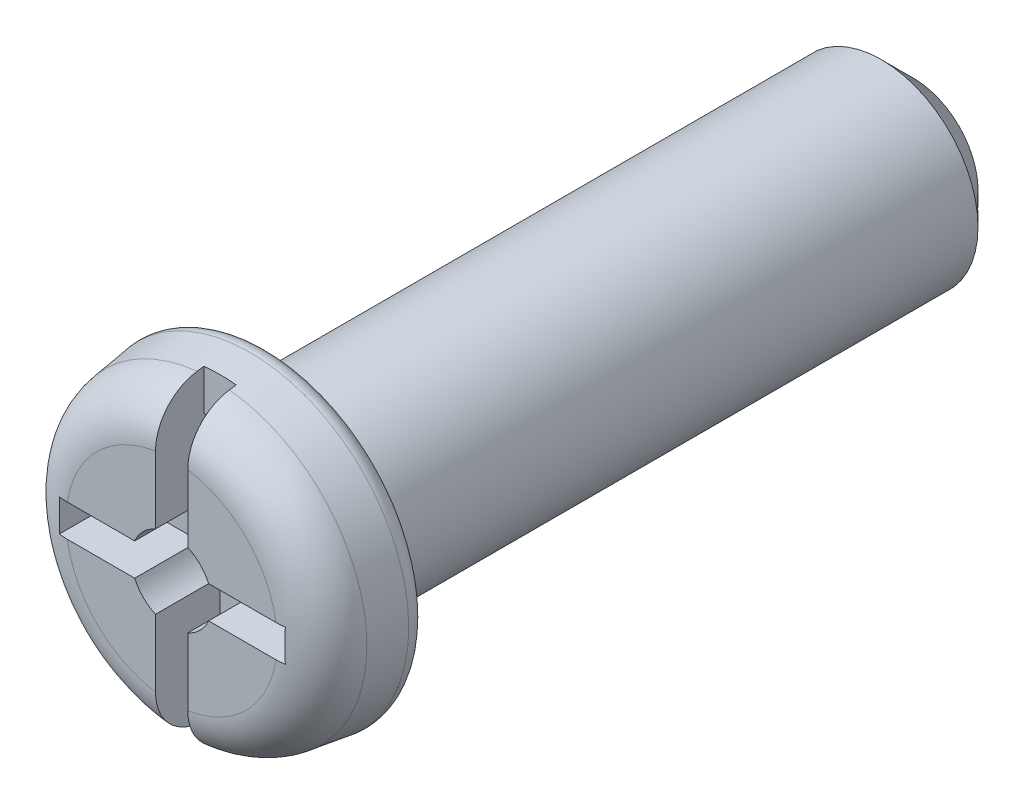
SolidWorks part; units mm, degrees
ref_plane "Plane1" through (0, 0, 0) normal (0, 0, 1) x (1, 0, 0)
ref_plane "Plane2" through (0, 0, 0) normal (0, 1, 0) x (1, 0, 0)
ref_plane "Plane3" through (0, 0, 0) normal (1, 0, 0) x (0, 0, -1)
sketch "Esquisse1" plane through (0, 0, 0) normal (0, 0, 1) x (1, 0, 0)
  circle A0 centre (0, 0) radius 2.5
  dimension "D1" = 5
extrude "Base-Extrusion" add sketch "Esquisse1" along normal blind 1.5 draft 8
fillet "Congé1" radius 0.75
fillet "Congé2" radius 0.25
sketch "Esquisse2" plane through (0, 0, 0) normal (0, 0, -1) x (-1, 0, 0)
  circle A0 centre (0, 0) radius 1.5
  dimension "D1" = 3
extrude "Boss.-Extru.1" add sketch "Esquisse2" along normal blind 10
chamfer "Chanfrein1" distance 0.5 angle 45
sketch "Esquisse4" plane through (0, 0, 1.5) normal (0, 0, 1) x (1, 0, 0)
  line L0 (0, 0) -> (0, 2) construction
  line L1 (-0.25, 1.75) -> (-0.25, 0.5728)
  line L2 (0.25, 1.75) -> (0.25, 0.5728)
  line L3 (-0.25, 1.75) -> (0.25, 1.75)
  line L4 (1.75, -0.25) -> (0.5728, -0.25)
  line L5 (1.75, 0.25) -> (1.75, -0.25)
  line L6 (1.75, 0.25) -> (0.5728, 0.25)
  line L7 (-0.25, -1.75) -> (-0.25, -0.5728)
  line L8 (0.25, -1.75) -> (-0.25, -1.75)
  line L9 (0.25, -1.75) -> (0.25, -0.5728)
  line L10 (-1.75, 0.25) -> (-0.5728, 0.25)
  line L11 (-1.75, -0.25) -> (-1.75, 0.25)
  line L12 (-1.75, -0.25) -> (-0.5728, -0.25)
  arc A0 (0.5728, 0.25) -> (0.25, 0.5728) centre (0, 0) ccw
  arc A1 (0.25, -0.5728) -> (0.5728, -0.25) centre (0, 0) ccw
  arc A2 (-0.5728, -0.25) -> (-0.25, -0.5728) centre (0, 0) ccw
  arc A3 (-0.25, 0.5728) -> (-0.5728, 0.25) centre (0, 0) ccw
  dimension "D1" = 1.25
  dimension "D2" = 0.5
  dimension "D3" = 1.75
extrude "Enlèv. mat.-Extru.1" cut sketch "Esquisse4" against normal blind 1
sketch "Esquisse5" plane through (0, 0, 1.5) normal (0, 0, 1) x (1, 0, 0)
  line L1 (-0.25, 2.5114) -> (0.25, 2.5114)
  line L2 (-0.25, 2.5114) -> (-0.25, -2.4889)
  line L3 (-0.25, -2.4889) -> (0.25, -2.4889)
  line L4 (0.25, 2.5114) -> (0.25, -2.4889)
extrude "Enlèv. mat.-Extru.2" cut sketch "Esquisse5" against normal blind 0.75
